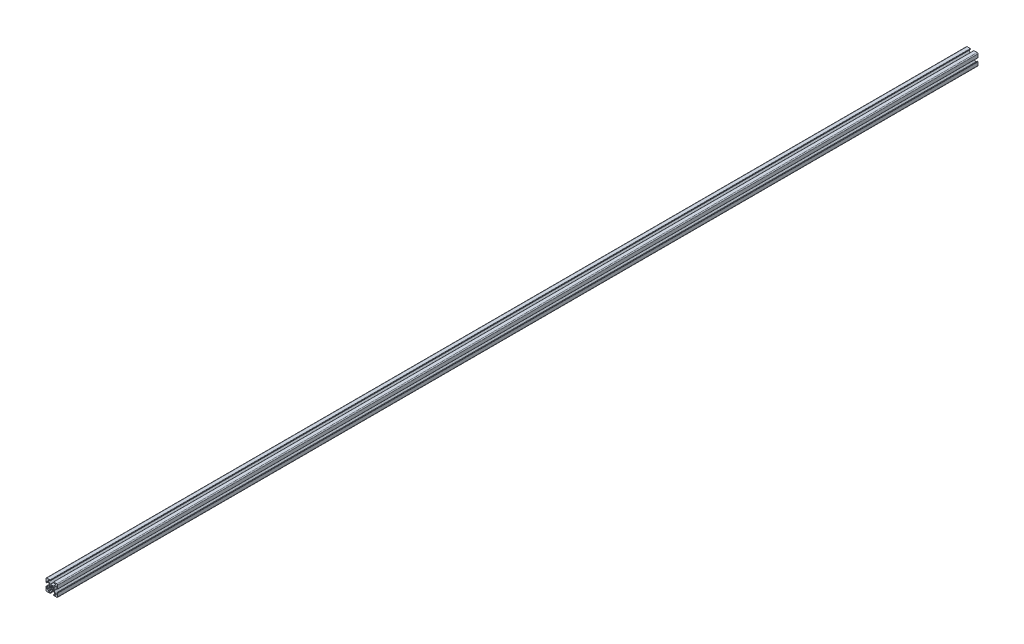
SolidWorks part; units mm, degrees
ref_plane "Front Plane" through (0, 0, 0) normal (0, 0, 1) x (1, 0, 0)
ref_plane "Top Plane" through (0, 0, 0) normal (0, 1, 0) x (1, 0, 0)
ref_plane "Right Plane" through (0, 0, 0) normal (1, 0, 0) x (0, 0, -1)
ref_plane "Plane1" through (0, 0, -457.2) normal (0, 0, -1) x (-1, 0, 0)
sketch "Sketch1" plane through (0, 0, -457.2) normal (0, 0, -1) x (-1, 0, 0)
  line L0 (2.3045, -2.1245) -> (2.1245, -2.3045)
  line L1 (-2.1245, -2.3045) -> (-2.3045, -2.1245)
  line L2 (-2.3045, 2.1245) -> (-2.1245, 2.3045)
  line L3 (2.1245, 2.3045) -> (2.3045, 2.1245)
  line L4 (10, -8.5) -> (10, -3.138)
  line L5 (9.492, -2.63) -> (9.008, -2.63)
  line L6 (8.5, -3.138) -> (8.5, -5.487)
  line L7 (7.992, -5.995) -> (7.2659, -5.995)
  line L8 (6.9067, -5.8462) -> (3.8038, -2.7433)
  line L9 (3.655, -2.3841) -> (3.655, 2.3838)
  line L10 (3.8038, 2.743) -> (6.907, 5.8462)
  line L11 (7.2662, 5.995) -> (7.992, 5.995)
  line L12 (8.5, 5.487) -> (8.5, 3.138)
  line L13 (9.008, 2.63) -> (9.492, 2.63)
  line L14 (10, 3.138) -> (10, 8.5)
  line L15 (8.5, 10) -> (3.138, 10)
  line L16 (2.63, 9.492) -> (2.63, 9.008)
  line L17 (3.138, 8.5) -> (5.487, 8.5)
  line L18 (5.995, 7.992) -> (5.995, 7.2659)
  line L19 (5.8462, 6.9067) -> (2.7433, 3.8038)
  line L20 (2.3841, 3.655) -> (-2.3838, 3.655)
  line L21 (-2.743, 3.8038) -> (-5.8462, 6.907)
  line L22 (-5.995, 7.2662) -> (-5.995, 7.992)
  line L23 (-5.487, 8.5) -> (-3.138, 8.5)
  line L24 (-2.63, 9.008) -> (-2.63, 9.492)
  line L25 (-3.138, 10) -> (-8.5, 10)
  line L26 (-10, 8.5) -> (-10, 3.138)
  line L27 (-9.492, 2.63) -> (-9.008, 2.63)
  line L28 (-8.5, 3.138) -> (-8.5, 5.487)
  line L29 (-7.992, 5.995) -> (-7.2659, 5.995)
  line L30 (-6.9067, 5.8462) -> (-3.8038, 2.7433)
  line L31 (-3.655, 2.3841) -> (-3.655, -2.3838)
  line L32 (-3.8038, -2.743) -> (-6.907, -5.8462)
  line L33 (-7.2662, -5.995) -> (-7.992, -5.995)
  line L34 (-8.5, -5.487) -> (-8.5, -3.138)
  line L35 (-9.008, -2.63) -> (-9.492, -2.63)
  line L36 (-10, -3.138) -> (-10, -8.5)
  line L37 (-8.5, -10) -> (-3.138, -10)
  line L38 (-2.63, -9.492) -> (-2.63, -9.008)
  line L39 (-3.138, -8.5) -> (-5.487, -8.5)
  line L40 (-5.995, -7.992) -> (-5.995, -7.2659)
  line L41 (-5.8462, -6.9067) -> (-2.7433, -3.8038)
  line L42 (-2.3841, -3.655) -> (2.3838, -3.655)
  line L43 (2.743, -3.8038) -> (5.8462, -6.907)
  line L44 (5.995, -7.2662) -> (5.995, -7.992)
  line L45 (5.487, -8.5) -> (3.138, -8.5)
  line L46 (2.63, -9.008) -> (2.63, -9.492)
  line L47 (3.138, -10) -> (8.5, -10)
  arc A0 (1.9358, 0.8037) -> (1.9358, -0.8037) centre (0, 0) cw
  arc A1 (1.9358, -0.8037) -> (2.3045, -2.1245) centre (1.748, -1.568) cw
  arc A2 (2.1245, -2.3045) -> (0.8037, -1.9358) centre (1.568, -1.748) cw
  arc A3 (0.8037, -1.9358) -> (-0.8037, -1.9358) centre (0, 0) cw
  arc A4 (-0.8037, -1.9358) -> (-2.1245, -2.3045) centre (-1.568, -1.748) cw
  arc A5 (-2.3045, -2.1245) -> (-1.9358, -0.8037) centre (-1.748, -1.568) cw
  arc A6 (-1.9358, -0.8037) -> (-1.9358, 0.8037) centre (0, 0) cw
  arc A7 (-1.9358, 0.8037) -> (-2.3045, 2.1245) centre (-1.748, 1.568) cw
  arc A8 (-2.1245, 2.3045) -> (-0.8037, 1.9358) centre (-1.568, 1.748) cw
  arc A9 (-0.8037, 1.9358) -> (0.8037, 1.9358) centre (0, 0) cw
  arc A10 (0.8037, 1.9358) -> (2.1245, 2.3045) centre (1.568, 1.748) cw
  arc A11 (2.3045, 2.1245) -> (1.9358, 0.8037) centre (1.748, 1.568) cw
  arc A12 (10, -3.138) -> (9.492, -2.63) centre (9.492, -3.138) ccw
  arc A13 (9.008, -2.63) -> (8.5, -3.138) centre (9.008, -3.138) ccw
  arc A14 (8.5, -5.487) -> (7.992, -5.995) centre (7.992, -5.487) cw
  arc A15 (7.2659, -5.995) -> (6.9067, -5.8462) centre (7.2659, -5.487) cw
  arc A16 (3.8038, -2.7433) -> (3.655, -2.3841) centre (4.163, -2.3841) cw
  arc A17 (3.655, 2.3838) -> (3.8038, 2.743) centre (4.163, 2.3838) cw
  arc A18 (6.907, 5.8462) -> (7.2662, 5.995) centre (7.2662, 5.487) cw
  arc A19 (7.992, 5.995) -> (8.5, 5.487) centre (7.992, 5.487) cw
  arc A20 (8.5, 3.138) -> (9.008, 2.63) centre (9.008, 3.138) ccw
  arc A21 (9.492, 2.63) -> (10, 3.138) centre (9.492, 3.138) ccw
  arc A22 (10, 8.5) -> (8.5, 10) centre (8.5, 8.5) ccw
  arc A23 (3.138, 10) -> (2.63, 9.492) centre (3.138, 9.492) ccw
  arc A24 (2.63, 9.008) -> (3.138, 8.5) centre (3.138, 9.008) ccw
  arc A25 (5.487, 8.5) -> (5.995, 7.992) centre (5.487, 7.992) cw
  arc A26 (5.995, 7.2659) -> (5.8462, 6.9067) centre (5.487, 7.2659) cw
  arc A27 (2.7433, 3.8038) -> (2.3841, 3.655) centre (2.3841, 4.163) cw
  arc A28 (-2.3838, 3.655) -> (-2.743, 3.8038) centre (-2.3838, 4.163) cw
  arc A29 (-5.8462, 6.907) -> (-5.995, 7.2662) centre (-5.487, 7.2662) cw
  arc A30 (-5.995, 7.992) -> (-5.487, 8.5) centre (-5.487, 7.992) cw
  arc A31 (-3.138, 8.5) -> (-2.63, 9.008) centre (-3.138, 9.008) ccw
  arc A32 (-2.63, 9.492) -> (-3.138, 10) centre (-3.138, 9.492) ccw
  arc A33 (-8.5, 10) -> (-10, 8.5) centre (-8.5, 8.5) ccw
  arc A34 (-10, 3.138) -> (-9.492, 2.63) centre (-9.492, 3.138) ccw
  arc A35 (-9.008, 2.63) -> (-8.5, 3.138) centre (-9.008, 3.138) ccw
  arc A36 (-8.5, 5.487) -> (-7.992, 5.995) centre (-7.992, 5.487) cw
  arc A37 (-7.2659, 5.995) -> (-6.9067, 5.8462) centre (-7.2659, 5.487) cw
  arc A38 (-3.8038, 2.7433) -> (-3.655, 2.3841) centre (-4.163, 2.3841) cw
  arc A39 (-3.655, -2.3838) -> (-3.8038, -2.743) centre (-4.163, -2.3838) cw
  arc A40 (-6.907, -5.8462) -> (-7.2662, -5.995) centre (-7.2662, -5.487) cw
  arc A41 (-7.992, -5.995) -> (-8.5, -5.487) centre (-7.992, -5.487) cw
  arc A42 (-8.5, -3.138) -> (-9.008, -2.63) centre (-9.008, -3.138) ccw
  arc A43 (-9.492, -2.63) -> (-10, -3.138) centre (-9.492, -3.138) ccw
  arc A44 (-10, -8.5) -> (-8.5, -10) centre (-8.5, -8.5) ccw
  arc A45 (-3.138, -10) -> (-2.63, -9.492) centre (-3.138, -9.492) ccw
  arc A46 (-2.63, -9.008) -> (-3.138, -8.5) centre (-3.138, -9.008) ccw
  arc A47 (-5.487, -8.5) -> (-5.995, -7.992) centre (-5.487, -7.992) cw
  arc A48 (-5.995, -7.2659) -> (-5.8462, -6.9067) centre (-5.487, -7.2659) cw
  arc A49 (-2.7433, -3.8038) -> (-2.3841, -3.655) centre (-2.3841, -4.163) cw
  arc A50 (2.3838, -3.655) -> (2.743, -3.8038) centre (2.3838, -4.163) cw
  arc A51 (5.8462, -6.907) -> (5.995, -7.2662) centre (5.487, -7.2662) cw
  arc A52 (5.995, -7.992) -> (5.487, -8.5) centre (5.487, -7.992) cw
  arc A53 (3.138, -8.5) -> (2.63, -9.008) centre (3.138, -9.008) ccw
  arc A54 (2.63, -9.492) -> (3.138, -10) centre (3.138, -9.492) ccw
  arc A55 (8.5, -10) -> (10, -8.5) centre (8.5, -8.5) ccw
extrude "Boss-Extrude1" add sketch "Sketch1" against normal blind 1567.18
